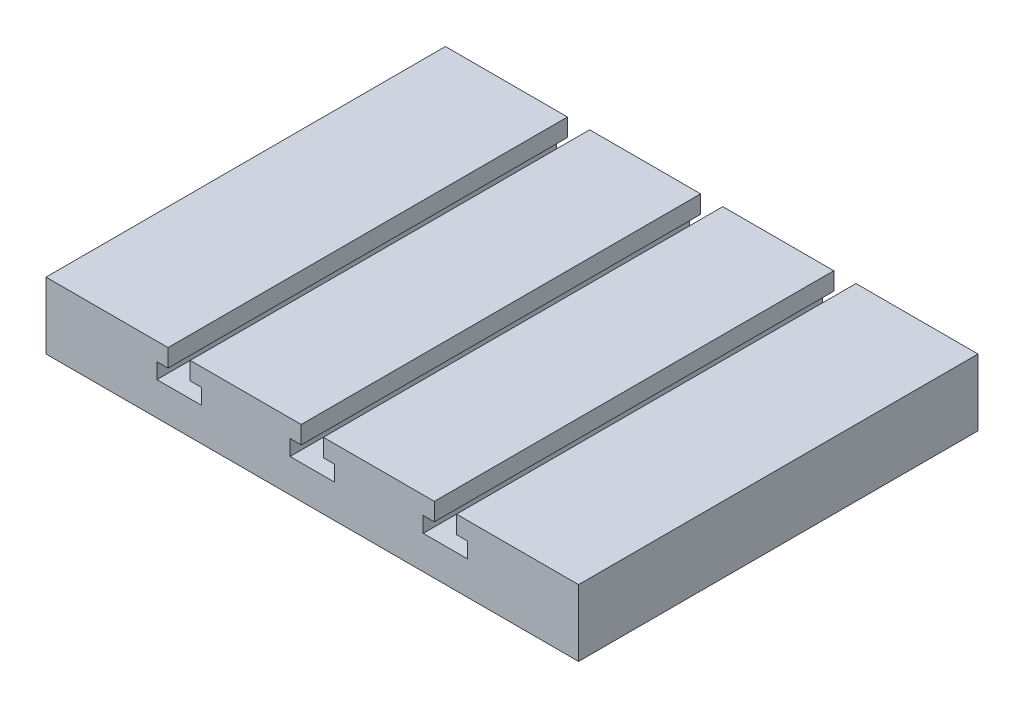
SolidWorks part; units mm, degrees
ref_plane "Front Plane" through (0, 0, 0) normal (0, 0, 1) x (1, 0, 0)
ref_plane "Top Plane" through (0, 0, 0) normal (0, 1, 0) x (1, 0, 0)
ref_plane "Right Plane" through (0, 0, 0) normal (1, 0, 0) x (0, 0, -1)
sketch "Sketch3" plane through (0, 0, 0) normal (0, 0, 1) x (1, 0, 0)
  line L1 (60, 7.5) -> (-60, 7.5)
  line L2 (60, 7.5) -> (60, -7.5)
  line L3 (60, -7.5) -> (-60, -7.5)
  line L4 (-60, 7.5) -> (-60, -7.5)
  line L5 (60, 7.5) -> (-60, -7.5) construction
  line L6 (60, -7.5) -> (-60, 7.5) construction
  point P0 (0, 0)
  dimension "D1" = 15
  dimension "D2" = 120
extrude "Boss-Extrude2" add sketch "Sketch3" along normal blind 90
sketch "Sketch6" plane through (0, 0, 90) normal (0, 0, 1) x (1, 0, 0)
  line L0 (32.5, 3.5) -> (35, 3.5)
  line L1 (-27.5, 3.5) -> (-25, 3.5)
  line L2 (-32.5, 7.5) -> (-27.5, 7.5)
  line L3 (-2.5, 7.5) -> (2.5, 7.5)
  line L4 (27.5, 7.5) -> (32.5, 7.5)
  line L5 (-32.5, 7.5) -> (-32.5, 3.5)
  line L6 (27.5, 7.5) -> (27.5, 3.5)
  line L7 (-27.5, 7.5) -> (-27.5, 3.5)
  line L8 (32.5, 7.5) -> (32.5, 3.5)
  line L9 (-35, 0) -> (-25, 0)
  line L12 (-2.5, 7.5) -> (-2.5, 3.5)
  line L13 (2.5, 7.5) -> (2.5, 3.5)
  line L14 (-35, 3.5) -> (-32.5, 3.5)
  line L15 (-35, 3.5) -> (-35, 0)
  line L16 (-5, 3.5) -> (-5, 0)
  line L17 (25, 3.5) -> (25, 0)
  line L18 (-25, 3.5) -> (-25, 0)
  line L19 (5, 3.5) -> (5, 0)
  line L20 (35, 3.5) -> (35, 0)
  line L21 (-60, 3.5) -> (60, 3.5) construction
  line L22 (-60, 0) -> (60, 0) construction
  line L28 (25, 0) -> (35, 0)
  line L29 (25, 3.5) -> (27.5, 3.5)
  line L35 (-5, 0) -> (5, 0)
  line L36 (-5, 3.5) -> (-2.5, 3.5)
  line L42 (2.5, 3.5) -> (5, 3.5)
  dimension "D7" = 3.5
extrude "Cut-Extrude1" cut sketch "Sketch6" against normal blind 90
